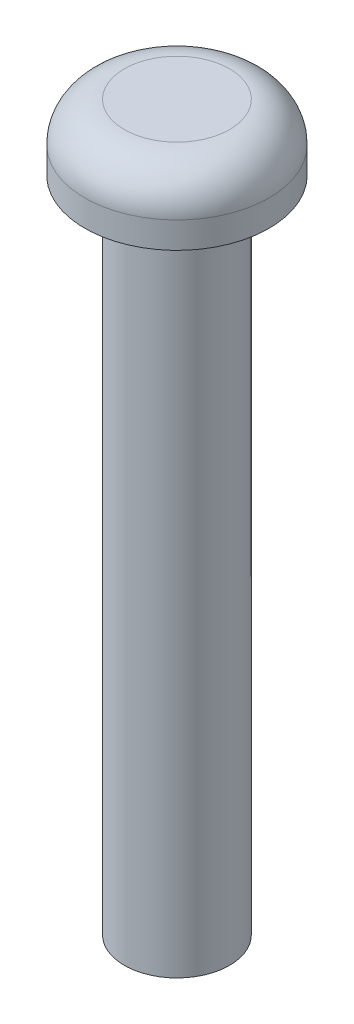
SolidWorks part; units mm, degrees
ref_plane "Front Plane" through (0, 0, 0) normal (0, 0, 1) x (1, 0, 0)
ref_plane "Top Plane" through (0, 0, 0) normal (0, 1, 0) x (1, 0, 0)
ref_plane "Right Plane" through (0, 0, 0) normal (1, 0, 0) x (0, 0, -1)
sketch "Sketch1" plane through (0, 0, 0) normal (0, 0, 1) x (1, 0, 0)
  line L0 (2, 0) -> (3.5, 0)
  line L1 (3.5, 0) -> (3.5, 1)
  line L2 (2, 2.5) -> (0, 2.5)
  line L3 (2, 0) -> (2, -25)
  line L4 (2, -25) -> (0, -25)
  line L5 (0, -25) -> (0, 2.5)
  arc A0 (3.5, 1) -> (2, 2.5) centre (2, 1) ccw
  dimension "D1" = 2
  dimension "D2" = 25
  dimension "D3" = 3.5
  dimension "D4" = 2.5
revolve "Revolve1" add sketch "Sketch1" angle 360 about L5
